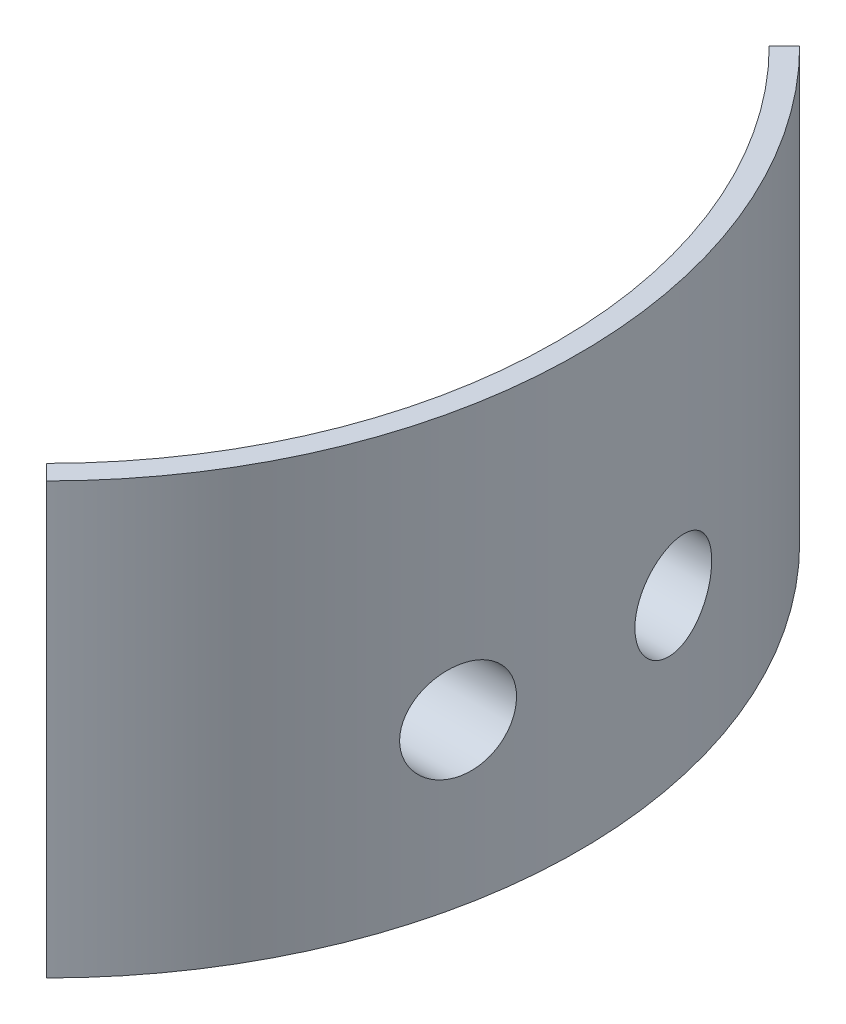
SolidWorks part; units mm, degrees
ref_plane "Front Plane" through (0, 0, 0) normal (0, 0, 1) x (1, 0, 0)
ref_plane "Top Plane" through (0, 0, 0) normal (0, 1, 0) x (1, 0, 0)
ref_plane "Right Plane" through (0, 0, 0) normal (1, 0, 0) x (0, 0, -1)
ref_axis "Axis1" through (0, -0.2847, 0) along (0, 1, 0)
ref_plane "SupportPlain" through (0, 10, 0) normal (0, 1, 0) x (1, 0, 0)
sketch "Sketch1" plane through (0, 0, 0) normal (0, 0, 1) x (1, 0, 0)
  line L0 (49.5, 0) -> (49.5, 40)
  line L5 (49.5, 40) -> (47.5, 40)
  line L6 (47.5, 40) -> (47.5, 0)
  line L7 (47.5, 0) -> (49.5, 0)
  point P9 (48.5, 0)
  dimension "D1" = 40
  dimension "D2" = 2
  dimension "D3" = 49.5
revolve "Main" add sketch "Sketch1" angle 90 mid plane about axis through (0, -0.2847, 0) along (0, 1, 0)
sketch "Sketch2" plane through (0, 10, 0) normal (0, -1, 0) x (-1, 0, 0)
  line L0 (-47.2361, -5) -> (-33, -5)
  line L1 (-45.0694, -15) -> (-30, -15)
  line L2 (-33.5876, -33.5876) -> (-33.5876, 33.5876) construction
  line L9 (-47.2361, 5) -> (-33, 5)
  line L10 (-30, -15) -> (-30, 15)
  line L11 (-30, 15) -> (-45.0694, 15)
  line L13 (-33, 5) -> (-33, -5)
  arc A0 (-47.2361, 5) -> (-45.0694, 15) centre (0, 0) cw
  circle A1 centre (0, 0) radius 50 construction
  arc A2 (-45.0694, -15) -> (-47.2361, -5) centre (0, 0) cw
  circle A3 centre (0, 0) radius 47.5 construction
  point P4 (0, 0)
  point P7 (0, 0)
  point P26 (-30, 0)
  dimension "D7" = 10
  dimension "D4" = 100
  dimension "D1" = 10
  dimension "D2" = 30
  dimension "D3" = 3
  dimension "D8" = 10
extrude "Support" add sketch "Sketch2" against normal blind 10
sketch "Sketch6" plane through (0, 10, 0) normal (0, 1, 0) x (1, 0, 0)
  line L0 (30, -15) -> (30, 15) construction
  line L1 (29, -8.55) -> (30, -8.55)
  line L2 (29, -8.55) -> (29, -11.45)
  line L3 (29, -11.45) -> (30, -11.45)
  line L4 (30, -8.55) -> (30, -11.45)
  line L6 (29, 11.45) -> (30, 11.45)
  line L7 (29, 11.45) -> (29, 8.55)
  line L8 (29, 8.55) -> (30, 8.55)
  line L9 (30, 11.45) -> (30, 8.55)
  line L11 (30, -15) -> (30, 15) construction
  point P10 (30, -15)
  point P13 (30, 15)
  dimension "D1" = 3.55
  dimension "D2" = 2.9
  dimension "D3" = 1
  dimension "D4" = 3.55
extrude "Fix" add sketch "Sketch6" along normal up to surface (10 mm away) up to face at (38.8939, 20, 0)
sketch "Sketch9" plane through (33, 0, 0) normal (1, 0, 0) x (0, 0, -1)
  line L0 (11.45, 10) -> (8.55, 10) construction
  line L1 (15, 20) -> (15, 10) construction
  line L2 (-15, 20) -> (-15, 10) construction
  circle A0 centre (10, 15) radius 1.6
  circle A1 centre (-10, 15) radius 1.6
  dimension "D1" = 3.2
  dimension "D2" = 3.2
  dimension "D3" = 5
  dimension "D4" = 5
  dimension "D5" = 5
extrude "Holes" cut sketch "Sketch9" against normal through all
sketch "Sketch10" plane through (33, 0, 0) normal (1, 0, 0) x (0, 0, -1)
  circle A0 centre (10, 15) radius 4.5
  circle A1 centre (-10, 15) radius 4.5
  arc A2 (8.55, 14.3236) -> (11.45, 14.3236) centre (10, 15) ccw construction
  arc A3 (-11.45, 14.3236) -> (-8.55, 14.3236) centre (-10, 15) ccw construction
  dimension "D1" = 9
extrude "BigHoles" cut sketch "Sketch10" along normal through all
